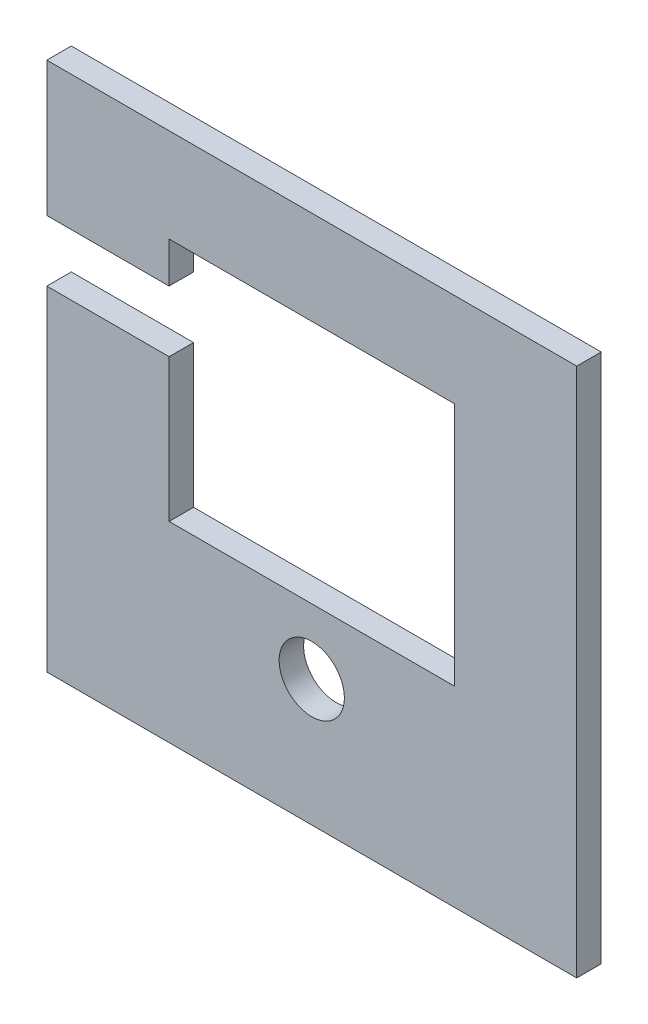
SolidWorks part; units mm, degrees
ref_plane "Piano frontale" through (0, 0, 0) normal (0, 0, 1) x (1, 0, 0)
ref_plane "Piano superiore" through (0, 0, 0) normal (0, 1, 0) x (1, 0, 0)
ref_plane "Piano destro" through (0, 0, 0) normal (1, 0, 0) x (0, 0, -1)
sketch "Schizzo1" plane through (0, 0, 0) normal (0, 0, 1) x (1, 0, 0)
  line L1 (65, -65) -> (-65, -65)
  line L2 (65, -65) -> (65, 65)
  line L3 (65, 65) -> (-65, 65)
  line L4 (-65, -65) -> (-65, 65)
  line L5 (65, -65) -> (-65, 65) construction
  line L6 (65, 65) -> (-65, -65) construction
  point P0 (0, 0)
  dimension "D1" = 130
  dimension "D2" = 130
extrude "Estrusione-Estrusione1" add sketch "Schizzo1" along normal blind 6
sketch "Schizzo2" plane through (0, 0, 6) normal (0, 0, 1) x (1, 0, 0)
  line L2 (35, -18) -> (-35, -18)
  line L3 (35, -18) -> (35, 42)
  line L4 (35, 42) -> (-35, 42)
  line L5 (-35, -18) -> (-35, 42)
  line L6 (35, -18) -> (-35, 42) construction
  line L7 (35, 42) -> (-35, -18) construction
  line L8 (65, 65) -> (-65, 65) construction
  line L10 (-65, 65) -> (-65, -65) construction
  point P2 (0, 0)
  dimension "D1" = 70
  dimension "D2" = 60
  dimension "D3" = 23
  dimension "D4" = 30
extrude "Taglio-Estrusione1" cut sketch "Schizzo2" against normal blind 15
sketch "Schizzo3" plane through (0, 0, 6) normal (0, 0, 1) x (1, 0, 0)
  line L0 (-35, -18) -> (-65, -18) construction
  line L1 (-65, 65) -> (-65, -65) construction
  line L2 (-65, -18) -> (65, -65) construction
  line L3 (35, -18) -> (65, -18) construction
  line L4 (65, -65) -> (65, 65) construction
  line L5 (-65, -65) -> (65, -18) construction
  line L6 (-35, -18) -> (35, -18) construction
  circle A0 centre (0, -34) radius 8
  point P4 (0, -18)
  dimension "D1" = 16
  dimension "D2" = 16
extrude "Taglio-Estrusione2" cut sketch "Schizzo3" against normal blind 15
sketch "Schizzo4" plane through (0, 0, 6) normal (0, 0, 1) x (1, 0, 0)
  line L0 (65, 65) -> (-65, 65) construction
  line L1 (-65, 32) -> (-35, 32)
  line L2 (-65, 32) -> (-65, 17)
  line L3 (-65, 17) -> (-35, 17)
  line L4 (-35, 32) -> (-35, 17)
  line L5 (-65, 32) -> (-35, 17) construction
  line L6 (-65, 17) -> (-35, 32) construction
  line L7 (-65, 65) -> (-65, -65) construction
  point P0 (-50, 24.5)
  dimension "D1" = 30
  dimension "D2" = 15
  dimension "D3" = 33
  dimension "D4" = 0
extrude "Taglio-Estrusione3" cut sketch "Schizzo4" against normal blind 15
